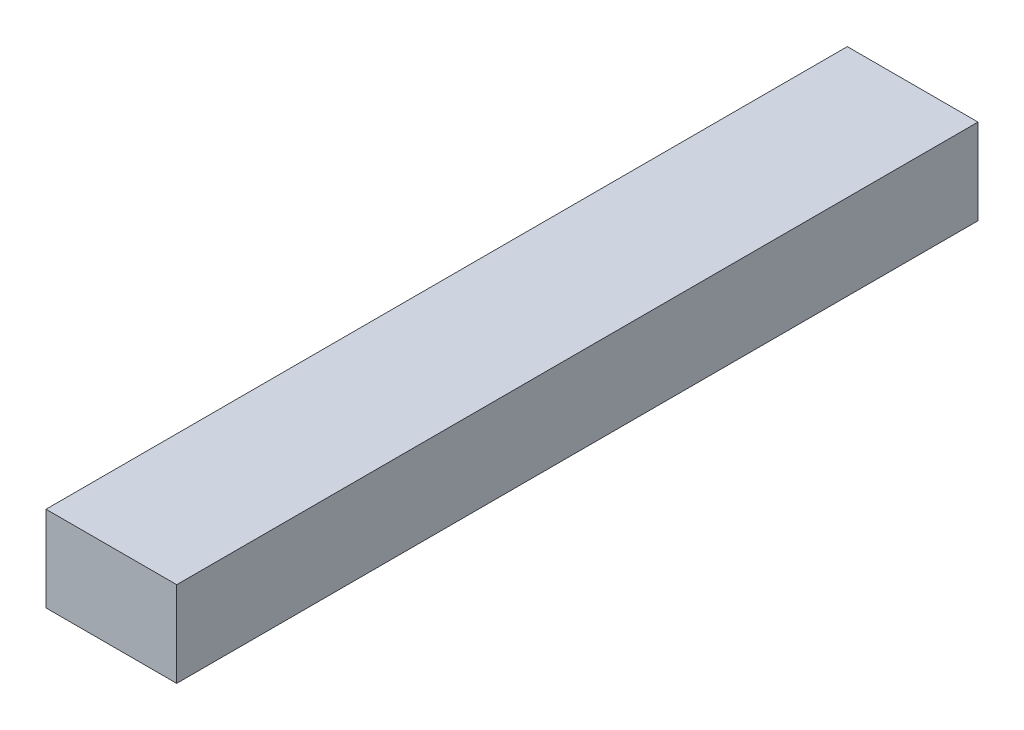
SolidWorks part; units mm, degrees
ref_plane "Plan de face" through (0, 0, 0) normal (0, 0, 1) x (1, 0, 0)
ref_plane "Plan de dessus" through (0, 0, 0) normal (0, 1, 0) x (1, 0, 0)
ref_plane "Plan de droite" through (0, 0, 0) normal (1, 0, 0) x (0, 0, -1)
sketch "Esquisse1" plane through (0, 0, 0) normal (0, 0, 1) x (1, 0, 0)
  line L1 (0, 0) -> (33.6, 0)
  line L2 (0, 0) -> (0, 21.98)
  line L3 (0, 21.98) -> (33.6, 21.98)
  line L4 (33.6, 0) -> (33.6, 21.98)
  dimension "D1" = 21.98
  dimension "D2" = 33.6
extrude "Boss.-Extru.1" add sketch "Esquisse1" along normal blind 206
